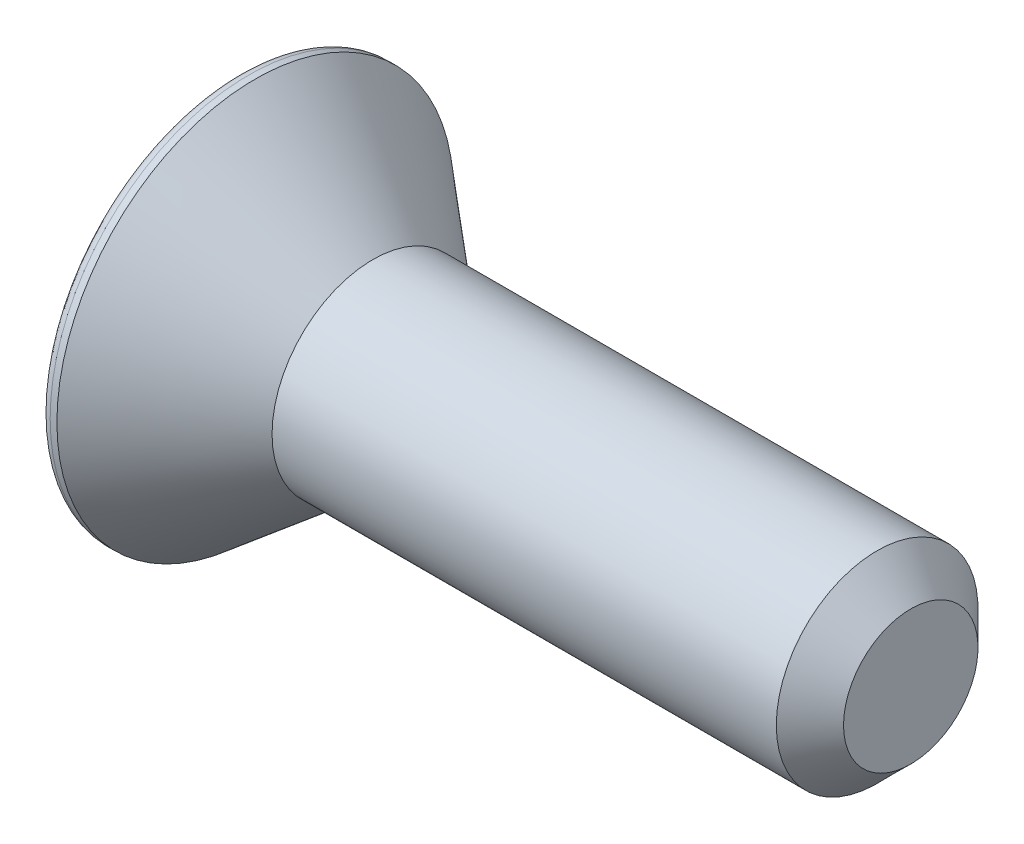
SolidWorks part; units mm, degrees
ref_plane "Спереди" through (0, 0, 0) normal (0, 0, 1) x (1, 0, 0)
ref_plane "Сверху" through (0, 0, 0) normal (0, 1, 0) x (1, 0, 0)
ref_plane "Справа" through (0, 0, 0) normal (1, 0, 0) x (0, 0, -1)
sketch "Эскиз1" plane through (0, 0, 0) normal (0, 0, 1) x (1, 0, 0)
  line L0 (0, 0) -> (0, 5.9)
  line L1 (0.5, 5.9) -> (4, 3)
  line L3 (4, 3) -> (20, 3)
  line L4 (20, 3) -> (20, 0)
  line L6 (0, 0) -> (20, 0)
  line L8 (0, 5.9) -> (0.5, 5.9)
  line L9 (0, 0) -> (-3.6011, 0) construction
  dimension "D4" = 0.5
  dimension "D1" = 4
  dimension "D2" = 11.8
  dimension "D3" = 6
  dimension "D5" = 20
revolve "Повернуть1" add sketch "Эскиз1" angle 360 about L6
cosmetic thread "Условное изображение резьбы1" parameters "D2"=4.891
sketch "Эскиз2" plane through (0, 0, 0) normal (-1, 0, 0) x (0, 0, 1)
  line L1 (1.1547, 2) -> (-1.1547, 2)
  line L2 (-1.1547, 2) -> (-2.3094, 0)
  line L3 (-2.3094, 0) -> (-1.1547, -2)
  line L4 (-1.1547, -2) -> (1.1547, -2)
  line L5 (1.1547, -2) -> (2.3094, 0)
  line L6 (2.3094, 0) -> (1.1547, 2)
  circle A0 centre (0, 0) radius 2 construction
  dimension "D1" = 4
extrude "Вырез-Вытянуть1" cut sketch "Эскиз2" against normal blind 3
fillet "Скругление1" radius 0.3 1 edges at (0, 0, 5.9)
chamfer "Фаска1" distance 1 angle 45 1 edges at (20, 0, 3)
